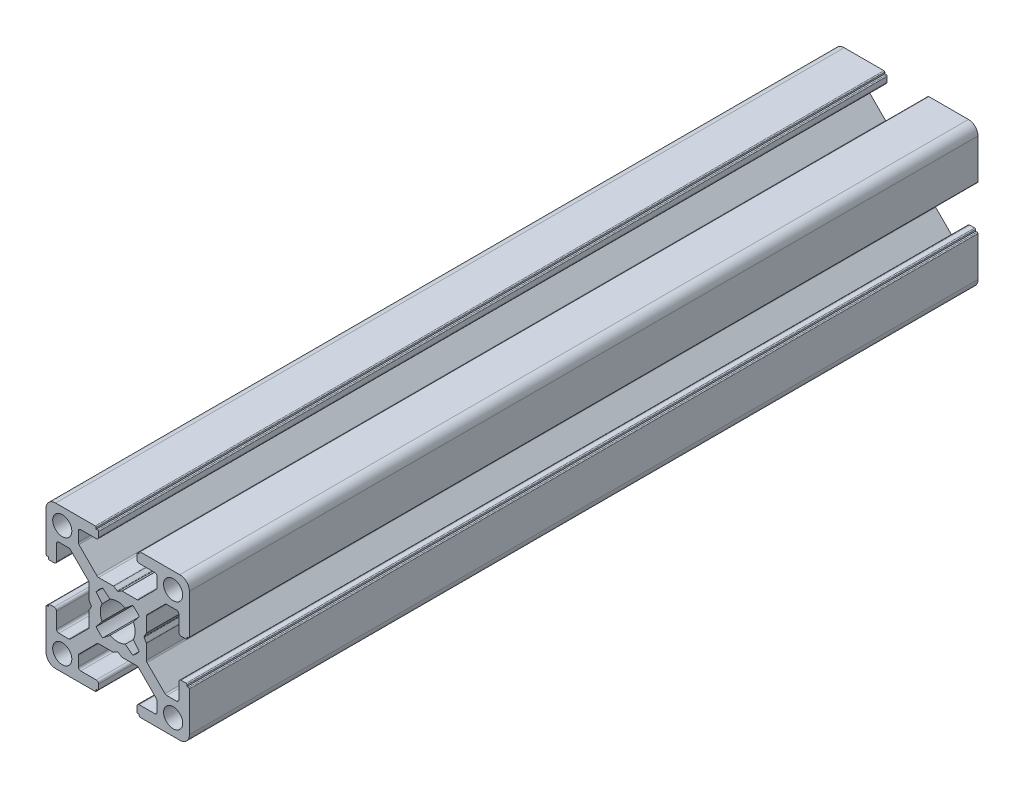
SolidWorks part; units mm, degrees
ref_plane "Alzado" through (0, 0, 0) normal (0, 0, 1) x (1, 0, 0)
ref_plane "Planta" through (0, 0, 0) normal (0, 1, 0) x (1, 0, 0)
ref_plane "Vista lateral" through (0, 0, 0) normal (1, 0, 0) x (0, 0, -1)
ref_plane "Plano1" through (0, 0, 1000) normal (0, 0, 1) x (1, 0, 0)
sketch "Croquis1" plane through (0, 0, 1000) normal (0, 0, 1) x (1, 0, 0)
  line L16 (-7.8359, -10.4816) -> (-6.3001, -11.7194)
  line L17 (-3.0999, -11.7194) -> (-1.5641, -10.4816)
  line L18 (-0.1947, -11.8453) -> (-1.4194, -13.3999)
  line L19 (-1.4194, -16.6001) -> (-0.1947, -18.1547)
  line L20 (-1.5641, -19.5184) -> (-3.0999, -18.2806)
  line L21 (-6.3001, -18.2806) -> (-7.8359, -19.5184)
  line L22 (-9.2053, -18.1547) -> (-7.9806, -16.6001)
  line L23 (-7.9806, -13.3999) -> (-9.2053, -11.8453)
  line L24 (9.8, -10.5) -> (10.1, -10.5)
  line L25 (10.3, -10.3) -> (10.3, -2)
  line L26 (8.3, 0) -> (0, 0)
  line L27 (-0.2, -0.2) -> (-0.2, -0.5)
  line L28 (-0.2, -0.5) -> (-0.5, -0.5)
  line L29 (-0.7, -0.7) -> (-0.7, -1.7)
  line L30 (-0.2, -2.2) -> (3.05, -2.2)
  line L31 (3.55, -2.7) -> (3.55, -4.7431)
  line L32 (3.4037, -5.0964) -> (-0.3491, -8.8534)
  line L33 (-0.7028, -9) -> (-3.7468, -9)
  line L34 (-3.8462, -9.0264) -> (-4.6006, -9.4583)
  line L35 (-4.7994, -9.4583) -> (-5.5538, -9.0264)
  line L36 (-5.6532, -9) -> (-8.6972, -9)
  line L37 (-9.0509, -8.8534) -> (-12.8037, -5.0964)
  line L38 (-12.95, -4.7431) -> (-12.95, -2.7)
  line L39 (-12.45, -2.2) -> (-9.2, -2.2)
  line L40 (-8.7, -1.7) -> (-8.7, -0.7)
  line L41 (-8.9, -0.5) -> (-9.2, -0.5)
  line L42 (-9.2, -0.5) -> (-9.2, -0.2)
  line L43 (-9.4, 0) -> (-17.7, 0)
  line L44 (-19.7, -2) -> (-19.7, -10.3)
  line L45 (-19.5, -10.5) -> (-19.2, -10.5)
  line L46 (-19.2, -10.5) -> (-19.2, -10.8)
  line L47 (-19, -11) -> (-18, -11)
  line L48 (-17.5, -10.5) -> (-17.5, -7.25)
  line L49 (-17, -6.75) -> (-14.9569, -6.75)
  line L50 (-14.6036, -6.8963) -> (-10.8466, -10.6491)
  line L51 (-10.7, -11.0028) -> (-10.7, -14.0468)
  line L52 (-10.6736, -14.1462) -> (-10.2417, -14.9006)
  line L53 (-10.2417, -15.0994) -> (-10.6736, -15.8538)
  line L54 (-10.7, -15.9532) -> (-10.7, -18.9972)
  line L55 (-10.8466, -19.3509) -> (-14.6036, -23.1037)
  line L56 (-14.9569, -23.25) -> (-17, -23.25)
  line L57 (-17.5, -22.75) -> (-17.5, -19.5)
  line L58 (-18, -19) -> (-19, -19)
  line L59 (-19.2, -19.2) -> (-19.2, -19.5)
  line L60 (-19.2, -19.5) -> (-19.5, -19.5)
  line L61 (-19.7, -19.7) -> (-19.7, -28)
  line L62 (-17.7, -30) -> (-9.4, -30)
  line L63 (-9.2, -29.8) -> (-9.2, -29.5)
  line L64 (-9.2, -29.5) -> (-8.9, -29.5)
  line L65 (-8.7, -29.3) -> (-8.7, -28.3)
  line L66 (-9.2, -27.8) -> (-12.45, -27.8)
  line L67 (-12.95, -27.3) -> (-12.95, -25.2569)
  line L68 (-12.8037, -24.9036) -> (-9.0509, -21.1466)
  line L69 (-8.6972, -21) -> (-5.6532, -21)
  line L70 (-5.5538, -20.9736) -> (-4.7994, -20.5417)
  line L71 (-4.6006, -20.5417) -> (-3.8462, -20.9736)
  line L72 (-3.7468, -21) -> (-0.7028, -21)
  line L73 (-0.3491, -21.1466) -> (3.4037, -24.9036)
  line L74 (3.55, -25.2569) -> (3.55, -27.3)
  line L75 (3.05, -27.8) -> (-0.2, -27.8)
  line L76 (-0.7, -28.3) -> (-0.7, -29.3)
  line L77 (-0.5, -29.5) -> (-0.2, -29.5)
  line L78 (-0.2, -29.5) -> (-0.2, -29.8)
  line L79 (0, -30) -> (8.3, -30)
  line L80 (10.3, -28) -> (10.3, -19.7)
  line L81 (10.1, -19.5) -> (9.8, -19.5)
  line L82 (9.8, -19.5) -> (9.8, -19.2)
  line L83 (9.6, -19) -> (8.6, -19)
  line L84 (8.1, -19.5) -> (8.1, -22.75)
  line L85 (7.6, -23.25) -> (5.5569, -23.25)
  line L86 (5.2036, -23.1037) -> (1.4466, -19.3509)
  line L87 (1.3, -18.9972) -> (1.3, -15.9532)
  line L88 (1.2736, -15.8538) -> (0.8417, -15.0994)
  line L89 (0.8417, -14.9006) -> (1.2736, -14.1462)
  line L90 (1.3, -14.0468) -> (1.3, -11.0028)
  line L91 (1.4466, -10.6491) -> (5.2036, -6.8963)
  line L92 (5.5569, -6.75) -> (7.6, -6.75)
  line L93 (8.1, -7.25) -> (8.1, -10.5)
  line L94 (8.6, -11) -> (9.6, -11)
  line L95 (9.8, -10.8) -> (9.8, -10.5)
  line L96 (8, -2.3) -> (5.8, -4.5) construction
  line L97 (-15.2, -2.3) -> (-17.4, -4.5) construction
  line L98 (-4.7, -15) -> (6.9, -15) construction
  arc A16 (-9.2053, -11.8453) -> (-7.8359, -10.4816) centre (-4.7, -15) cw
  arc A17 (-6.3001, -11.7194) -> (-3.0999, -11.7194) centre (-4.7, -15) cw
  arc A18 (-1.5641, -10.4816) -> (-0.1947, -11.8453) centre (-4.7, -15) cw
  arc A19 (-1.4194, -13.3999) -> (-1.4194, -16.6001) centre (-4.7, -15) cw
  arc A20 (-0.1947, -18.1547) -> (-1.5641, -19.5184) centre (-4.7, -15) cw
  arc A21 (-3.0999, -18.2806) -> (-6.3001, -18.2806) centre (-4.7, -15) cw
  arc A22 (-7.8359, -19.5184) -> (-9.2053, -18.1547) centre (-4.7, -15) cw
  arc A23 (-7.9806, -16.6001) -> (-7.9806, -13.3999) centre (-4.7, -15) cw
  arc A24 (10.1, -10.5) -> (10.3, -10.3) centre (10.1, -10.3) ccw
  arc A25 (10.3, -2) -> (8.3, 0) centre (8.3, -2) ccw
  arc A26 (0, 0) -> (-0.2, -0.2) centre (0, -0.2) ccw
  arc A27 (-0.5, -0.5) -> (-0.7, -0.7) centre (-0.5, -0.7) ccw
  arc A28 (-0.7, -1.7) -> (-0.2, -2.2) centre (-0.2, -1.7) ccw
  arc A29 (3.05, -2.2) -> (3.55, -2.7) centre (3.05, -2.7) cw
  arc A30 (3.55, -4.7431) -> (3.4037, -5.0964) centre (3.05, -4.7431) cw
  arc A31 (-0.3491, -8.8534) -> (-0.7028, -9) centre (-0.7028, -8.5) cw
  arc A32 (-3.7468, -9) -> (-3.8462, -9.0264) centre (-3.7468, -9.2) ccw
  arc A33 (-4.6006, -9.4583) -> (-4.7994, -9.4583) centre (-4.7, -9.2847) cw
  arc A34 (-5.5538, -9.0264) -> (-5.6532, -9) centre (-5.6532, -9.2) ccw
  arc A35 (-8.6972, -9) -> (-9.0509, -8.8534) centre (-8.6972, -8.5) cw
  arc A36 (-12.8037, -5.0964) -> (-12.95, -4.7431) centre (-12.45, -4.7431) cw
  arc A37 (-12.95, -2.7) -> (-12.45, -2.2) centre (-12.45, -2.7) cw
  arc A38 (-9.2, -2.2) -> (-8.7, -1.7) centre (-9.2, -1.7) ccw
  arc A39 (-8.7, -0.7) -> (-8.9, -0.5) centre (-8.9, -0.7) ccw
  arc A40 (-9.2, -0.2) -> (-9.4, 0) centre (-9.4, -0.2) ccw
  arc A41 (-17.7, 0) -> (-19.7, -2) centre (-17.7, -2) ccw
  arc A42 (-19.7, -10.3) -> (-19.5, -10.5) centre (-19.5, -10.3) ccw
  arc A43 (-19.2, -10.8) -> (-19, -11) centre (-19, -10.8) ccw
  arc A44 (-18, -11) -> (-17.5, -10.5) centre (-18, -10.5) ccw
  arc A45 (-17.5, -7.25) -> (-17, -6.75) centre (-17, -7.25) cw
  arc A46 (-14.9569, -6.75) -> (-14.6036, -6.8963) centre (-14.9569, -7.25) cw
  arc A47 (-10.8466, -10.6491) -> (-10.7, -11.0028) centre (-11.2, -11.0028) cw
  arc A48 (-10.7, -14.0468) -> (-10.6736, -14.1462) centre (-10.5, -14.0468) ccw
  arc A49 (-10.2417, -14.9006) -> (-10.2417, -15.0994) centre (-10.4153, -15) cw
  arc A50 (-10.6736, -15.8538) -> (-10.7, -15.9532) centre (-10.5, -15.9532) ccw
  arc A51 (-10.7, -18.9972) -> (-10.8466, -19.3509) centre (-11.2, -18.9972) cw
  arc A52 (-14.6036, -23.1037) -> (-14.9569, -23.25) centre (-14.9569, -22.75) cw
  arc A53 (-17, -23.25) -> (-17.5, -22.75) centre (-17, -22.75) cw
  arc A54 (-17.5, -19.5) -> (-18, -19) centre (-18, -19.5) ccw
  arc A55 (-19, -19) -> (-19.2, -19.2) centre (-19, -19.2) ccw
  arc A56 (-19.5, -19.5) -> (-19.7, -19.7) centre (-19.5, -19.7) ccw
  arc A57 (-19.7, -28) -> (-17.7, -30) centre (-17.7, -28) ccw
  arc A58 (-9.4, -30) -> (-9.2, -29.8) centre (-9.4, -29.8) ccw
  arc A59 (-8.9, -29.5) -> (-8.7, -29.3) centre (-8.9, -29.3) ccw
  arc A60 (-8.7, -28.3) -> (-9.2, -27.8) centre (-9.2, -28.3) ccw
  arc A61 (-12.45, -27.8) -> (-12.95, -27.3) centre (-12.45, -27.3) cw
  arc A62 (-12.95, -25.2569) -> (-12.8037, -24.9036) centre (-12.45, -25.2569) cw
  arc A63 (-9.0509, -21.1466) -> (-8.6972, -21) centre (-8.6972, -21.5) cw
  arc A64 (-5.6532, -21) -> (-5.5538, -20.9736) centre (-5.6532, -20.8) ccw
  arc A65 (-4.7994, -20.5417) -> (-4.6006, -20.5417) centre (-4.7, -20.7153) cw
  arc A66 (-3.8462, -20.9736) -> (-3.7468, -21) centre (-3.7468, -20.8) ccw
  arc A67 (-0.7028, -21) -> (-0.3491, -21.1466) centre (-0.7028, -21.5) cw
  arc A68 (3.4037, -24.9036) -> (3.55, -25.2569) centre (3.05, -25.2569) cw
  arc A69 (3.55, -27.3) -> (3.05, -27.8) centre (3.05, -27.3) cw
  arc A70 (-0.2, -27.8) -> (-0.7, -28.3) centre (-0.2, -28.3) ccw
  arc A71 (-0.7, -29.3) -> (-0.5, -29.5) centre (-0.5, -29.3) ccw
  arc A72 (-0.2, -29.8) -> (0, -30) centre (0, -29.8) ccw
  arc A73 (8.3, -30) -> (10.3, -28) centre (8.3, -28) ccw
  arc A74 (10.3, -19.7) -> (10.1, -19.5) centre (10.1, -19.7) ccw
  arc A75 (9.8, -19.2) -> (9.6, -19) centre (9.6, -19.2) ccw
  arc A76 (8.6, -19) -> (8.1, -19.5) centre (8.6, -19.5) ccw
  arc A77 (8.1, -22.75) -> (7.6, -23.25) centre (7.6, -22.75) cw
  arc A78 (5.5569, -23.25) -> (5.2036, -23.1037) centre (5.5569, -22.75) cw
  arc A79 (1.4466, -19.3509) -> (1.3, -18.9972) centre (1.8, -18.9972) cw
  arc A80 (1.3, -15.9532) -> (1.2736, -15.8538) centre (1.1, -15.9532) ccw
  arc A81 (0.8417, -15.0994) -> (0.8417, -14.9006) centre (1.0153, -15) cw
  arc A82 (1.2736, -14.1462) -> (1.3, -14.0468) centre (1.1, -14.0468) ccw
  arc A83 (1.3, -11.0028) -> (1.4466, -10.6491) centre (1.8, -11.0028) cw
  arc A84 (5.2036, -6.8963) -> (5.5569, -6.75) centre (5.5569, -7.25) cw
  arc A85 (7.6, -6.75) -> (8.1, -7.25) centre (7.6, -7.25) cw
  arc A86 (8.1, -10.5) -> (8.6, -11) centre (8.6, -10.5) ccw
  arc A87 (9.6, -11) -> (9.8, -10.8) centre (9.6, -10.8) ccw
  circle A88 centre (-16.3, -3.4) radius 2
  circle A89 centre (6.9, -3.4) radius 2
  circle A90 centre (-16.3, -26.6) radius 2
  circle A91 centre (6.9, -26.6) radius 2
  dimension "D3" = 4
  dimension "D1" = 30
  dimension "D2" = 30
  dimension "D4" = 23.2
  dimension "D5" = 23.2
extrude "Saliente-Extruir1" add sketch "Croquis1" against normal blind 165
